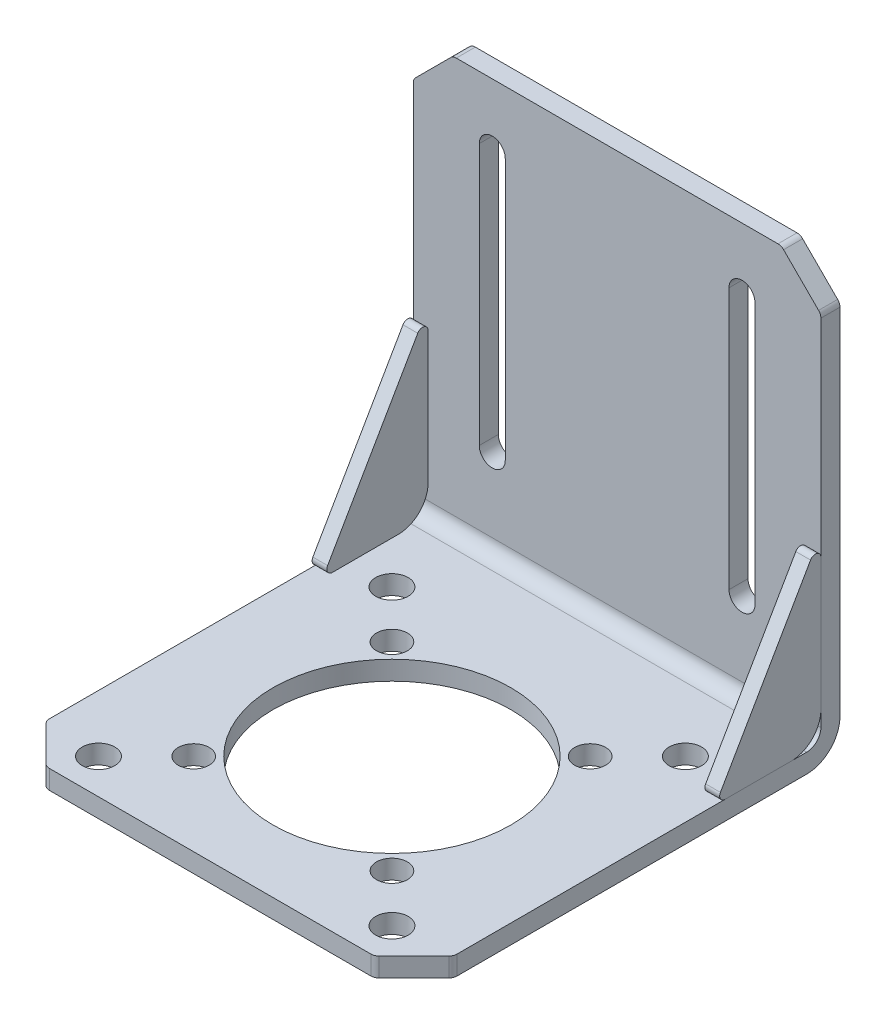
SolidWorks part; units mm, degrees
material "ASTM A36 Steel"
ref_plane "Front Plane" through (0, 0, 0) normal (0, 0, 1) x (1, 0, 0)
ref_plane "Top Plane" through (0, 0, 0) normal (0, 1, 0) x (1, 0, 0)
ref_plane "Right Plane" through (0, 0, 0) normal (1, 0, 0) x (0, 0, -1)
sketch "Sketch1" plane through (0, 0, 0) normal (0, 1, 0) x (1, 0, 0)
  line L0 (0, 0) -> (0, -19.05) construction
  line L1 (0, 0) -> (0, 19.05) construction
  line L2 (0, 0) -> (-19.05, 0) construction
  line L3 (0, 0) -> (19.05, 0) construction
  line L4 (0, -19.05) -> (0, -29.1084) construction
  line L5 (-26.289, -29.1084) -> (26.289, -29.1084)
  line L6 (26.289, -29.1084) -> (32.639, -29.1084) construction
  line L7 (32.639, -29.1084) -> (32.639, -22.7584) construction
  line L8 (-26.289, -29.1084) -> (-32.639, -29.1084) construction
  line L9 (-32.639, -29.1084) -> (-32.639, -22.7584) construction
  line L10 (-32.639, -22.7584) -> (-32.639, 39.116)
  line L11 (32.639, -22.7584) -> (32.639, 39.116)
  line L12 (-32.639, -22.7584) -> (-26.289, -29.1084)
  line L13 (32.639, -22.7584) -> (26.289, -29.1084)
  line L14 (0, 19.05) -> (0, 39.116) construction
  line L15 (-32.639, 39.116) -> (32.639, 39.116)
  circle A0 centre (0, 0) radius 19.05
  dimension "D1" = 38.1
  dimension "D3" = 6.35
  dimension "D2" = 10.0584
  dimension "D4" = 65.278
  dimension "D5" = 68.2244
extrude "Boss-Extrude1" add sketch "Sketch1" against normal blind 3.048
sketch "Sketch2" plane through (0, 0, 0) normal (0, 1, 0) x (1, 0, 0)
  line L0 (32.639, -22.7584) -> (32.639, 39.116) construction
  line L1 (-32.639, 39.116) -> (32.639, 39.116)
  line L2 (-32.639, 39.116) -> (-32.639, 36.068)
  line L3 (-32.639, 36.068) -> (32.639, 36.068)
  line L4 (32.639, 39.116) -> (32.639, 36.068)
  dimension "D1" = 3.048
extrude "Boss-Extrude2" add sketch "Sketch2" along normal offset from surface (65.9384 mm away) 68.9864 up to face at (0, -3.048, 19.05)
fillet "Fillet1" radius 2.286 1 edges at (0, 0, -36.068)
fillet "Fillet2" radius 5.334 1 edges at (0, -3.048, -39.116)
sketch "Sketch3" plane through (0, 0, -39.116) normal (0, 0, -1) x (-1, 0, 0)
  line L0 (0, 0) -> (0, 55.9181) construction
  line L1 (0, 55.9181) -> (0, 65.9384) construction
  line L2 (32.639, 65.9384) -> (-32.639, 65.9384) construction
  line L3 (-20, 55.9181) -> (20, 55.9181) construction
  line L4 (-20, 55.9181) -> (-20, 14.0462) construction
  line L5 (-17.9172, 55.9181) -> (-17.9172, 14.0462)
  line L6 (-22.0828, 55.9181) -> (-22.0828, 14.0462)
  line L7 (20, 55.9181) -> (20, 14.0462) construction
  line L8 (22.0828, 55.9181) -> (22.0828, 14.0462)
  line L9 (17.9172, 55.9181) -> (17.9172, 14.0462)
  line L10 (-20, 55.9181) -> (-20, 58.0009) construction
  line L11 (20, 55.9181) -> (20, 58.0009) construction
  line L12 (-20, 14.0462) -> (-20, 11.9634) construction
  line L13 (20, 14.0462) -> (20, 11.9634) construction
  arc A0 (-17.9172, 55.9181) -> (-22.0828, 55.9181) centre (-20, 55.9181) ccw
  arc A1 (-22.0828, 14.0462) -> (-17.9172, 14.0462) centre (-20, 14.0462) ccw
  arc A2 (22.0828, 55.9181) -> (17.9172, 55.9181) centre (20, 55.9181) ccw
  arc A3 (17.9172, 14.0462) -> (22.0828, 14.0462) centre (20, 14.0462) ccw
  point P8 (-20, 34.9821)
  point P14 (20, 34.9821)
  dimension "D1" = 40
  dimension "D2" = 4.1656
  dimension "D3" = 7.9375
  dimension "D4" = 46.0375
extrude "Cut-Extrude1" cut sketch "Sketch3" against normal up to surface (3.048 mm away) up to face at (0, 34.1122, -36.068)
chamfer "Chamfer1" distance 6.35 angle 45 2 edges at (32.639, 65.9384, -37.592) (-32.639, 65.9384, -37.592)
fillet "Fillet3" radius 1.27 8 edges at (-32.639, 59.5884, -37.592) (-26.289, 65.9384, -37.592) (26.289, 65.9384, -37.592) (32.639, 59.5884, -37.592) (32.639, -1.524, 22.7584) (26.289, -1.524, 29.1084) (-26.289, -1.524, 29.1084) (-32.639, -1.524, 22.7584)
sketch "Sketch6" plane through (0, 0, 0) normal (0, 1, 0) x (1, 0, 0)
  line L1 (-15.875, 15.875) -> (15.875, 15.875) construction
  line L2 (-15.875, 15.875) -> (-15.875, -15.875) construction
  line L3 (-15.875, -15.875) -> (15.875, -15.875) construction
  line L4 (15.875, 15.875) -> (15.875, -15.875) construction
  line L5 (-15.875, 15.875) -> (15.875, -15.875) construction
  line L6 (-15.875, -15.875) -> (15.875, 15.875) construction
  circle A0 centre (-15.875, -15.875) radius 2.4765
  circle A1 centre (15.875, -15.875) radius 2.4765
  circle A2 centre (15.875, 15.875) radius 2.4765
  circle A3 centre (-15.875, 15.875) radius 2.4765
  point P0 (0, 0)
  dimension "D2" = 4.953
  dimension "D1" = 31.75
  dimension "D3" = 31.75
extrude "Cut-Extrude2" cut sketch "Sketch6" against normal up to surface (3.048 mm away) up to face at (0, -3.048, 19.05)
sketch "Sketch7" plane through (0, 0, 0) normal (0, 1, 0) x (1, 0, 0)
  line L1 (-23.5, 23.5) -> (23.5, 23.5) construction
  line L2 (-23.5, 23.5) -> (-23.5, -23.5) construction
  line L3 (-23.5, -23.5) -> (23.5, -23.5) construction
  line L4 (23.5, 23.5) -> (23.5, -23.5) construction
  line L5 (-23.5, 23.5) -> (23.5, -23.5) construction
  line L6 (-23.5, -23.5) -> (23.5, 23.5) construction
  circle A0 centre (23.5, 23.5) radius 2.6035
  circle A1 centre (23.5, -23.5) radius 2.6035
  circle A2 centre (-23.5, -23.5) radius 2.6035
  circle A3 centre (-23.5, 23.5) radius 2.6035
  point P0 (0, 0)
  dimension "D3" = 5.207
  dimension "D1" = 47
  dimension "D2" = 47
extrude "Cut-Extrude3" cut sketch "Sketch7" against normal up to surface (3.048 mm away) up to face at (-15.875, -3.048, -18.3515)
sketch "Sketch4" plane through (32.639, 0, 0) normal (1, 0, 0) x (0, 0, -1)
  line L0 (36.068, 29.21) -> (36.068, 0)
  line L1 (36.068, 59.0623) -> (36.068, 2.286) construction
  line L2 (36.068, 0) -> (19.2036, 0)
  line L3 (-22.2323, 0) -> (33.782, 0) construction
  line L4 (19.2036, 0) -> (36.068, 29.21)
  dimension "D1" = 30
  dimension "D2" = 29.21
extrude "Boss-Extrude3" add sketch "Sketch4" against normal blind 2.3622 separate body
fillet "Fillet4" radius 0.889 2 edges at (31.4579, 29.21, -36.068) (31.4579, 0, -19.2036)
fillet "Fillet5" radius 4.7625 1 edges at (31.4579, 0, -36.068)
mirror "Mirror1" about plane through (0, 0, 0) normal (1, 0, 0) of bodies 104
sketch "Sketch8" plane through (0, 0, -39.116) normal (0, 0, -1) x (-1, 0, 0)
  line L0 (0, 0) -> (0, 34.925) construction
  line L1 (-17.9172, 34.925) -> (17.9172, 34.925) construction
  line L2 (-17.9172, 14.0462) -> (-17.9172, 55.9181) construction
  text T0 "NEMA 23\r\nMount" font "Calibri" height 3
  dimension "D1" = 34.925
extrude "Cut-Extrude5" cut sketch "Sketch8" against normal blind 0.1
